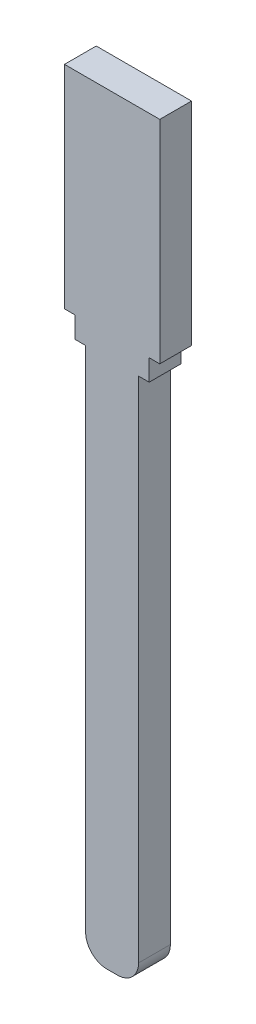
SolidWorks part; units mm, degrees
ref_plane "Alzado" through (0, 0, 0) normal (0, 0, 1) x (1, 0, 0)
ref_plane "Planta" through (0, 0, 0) normal (0, 1, 0) x (1, 0, 0)
ref_plane "Vista lateral" through (0, 0, 0) normal (1, 0, 0) x (0, 0, -1)
sketch "Model" plane through (0, 0, 0) normal (0, 0, 1) x (1, 0, 0)
  line L0 (-36.4136, 21.5) -> (-36.4136, 15.5)
  line L1 (-36.4136, 15.5) -> (-36.4136, 1.5)
  line L2 (-36.4136, 1.5) -> (-37.4136, 1.5)
  line L3 (-37.4136, 1.5) -> (-37.4136, -0.5)
  line L4 (-37.4136, -0.5) -> (-38.4136, -0.5)
  line L5 (-38.4136, -0.5) -> (-38.4136, -48.5)
  line L6 (-40.4136, -50.5) -> (-41.4136, -50.5)
  line L7 (-43.4136, -48.5) -> (-43.4136, -0.5)
  line L8 (-43.4136, -0.5) -> (-44.4136, -0.5)
  line L9 (-44.4136, -0.5) -> (-44.4136, 1.5)
  line L10 (-44.4136, 1.5) -> (-45.4136, 1.5)
  line L11 (-45.4136, 1.5) -> (-45.4136, 21.5)
  line L12 (-45.4136, 21.5) -> (-36.4136, 21.5)
  arc A0 (-40.4136, -50.5) -> (-38.4136, -48.5) centre (-40.4136, -48.5) ccw
  arc A1 (-43.4136, -48.5) -> (-41.4136, -50.5) centre (-41.4136, -48.5) ccw
extrude "Saliente-Extruir1" add sketch "Model" along normal blind 3
